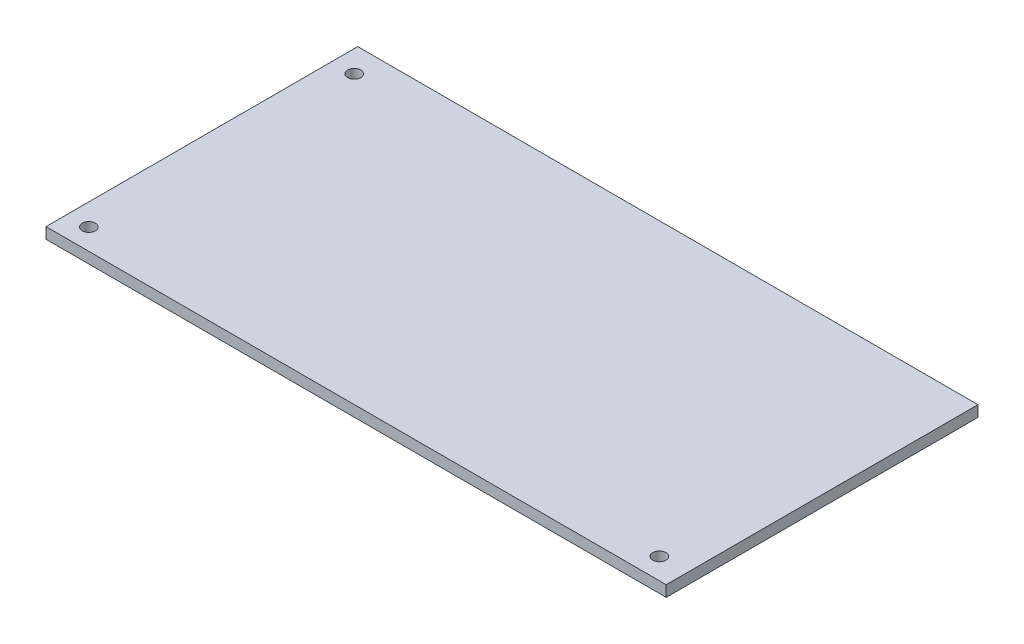
SolidWorks part; units mm, degrees
ref_plane "Plano frontal" through (0, 0, 0) normal (0, 0, 1) x (1, 0, 0)
ref_plane "Plano superior" through (0, 0, 0) normal (0, 1, 0) x (1, 0, 0)
ref_plane "Plano direito" through (0, 0, 0) normal (1, 0, 0) x (0, 0, -1)
sketch "Esboço1" plane through (0, 0, 0) normal (0, 1, 0) x (1, 0, 0)
  line L1 (0, 0) -> (93.5, 0)
  line L2 (0, 0) -> (0, 47)
  line L3 (0, 47) -> (93.5, 47)
  line L4 (93.5, 0) -> (93.5, 47)
  dimension "D1" = 93.5
  dimension "D2" = 47
extrude "Ressalto-extrusão1" add sketch "Esboço1" along normal blind 1.66
sketch "Esboço2" plane through (0, 1.66, 0) normal (0, 1, 0) x (1, 0, 0)
  line L0 (3.2838, 47) -> (3.2838, 0) construction
  line L1 (93.5, 47) -> (0, 47) construction
  line L2 (0, 0) -> (93.5, 0) construction
  line L3 (0, 3.1797) -> (93.5, 3.1797) construction
  line L4 (0, 47) -> (0, 0) construction
  line L5 (93.5, 0) -> (93.5, 47) construction
  circle A0 centre (3.2838, 43.1797) radius 1
  circle A1 centre (89.2838, 3.1797) radius 1
  circle A2 centre (3.2838, 3.1797) radius 1
  point P18 (3.2838, 3.1797)
  dimension "D1" = 2
  dimension "D2" = 2
  dimension "D3" = 2
  dimension "D5" = 40
  dimension "D4" = 86
extrude "Corte-extrusão1" cut sketch "Esboço2" against normal blind 1.66
